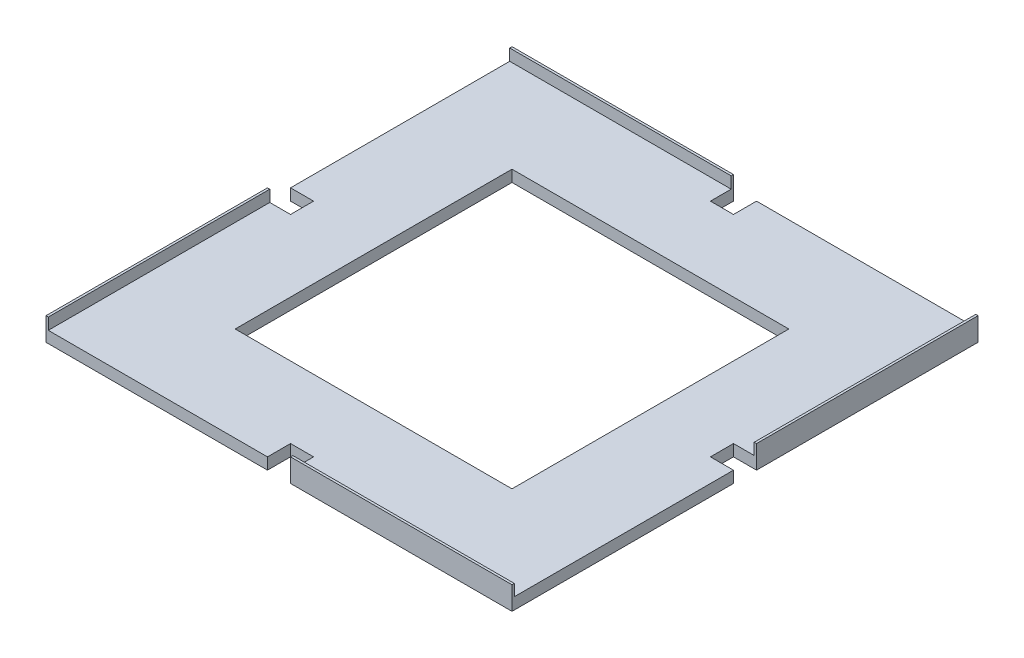
SolidWorks part; units mm, degrees
ref_plane "Front Plane" through (0, 0, 0) normal (0, 0, 1) x (1, 0, 0)
ref_plane "Top Plane" through (0, 0, 0) normal (0, 1, 0) x (1, 0, 0)
ref_plane "Right Plane" through (0, 0, 0) normal (1, 0, 0) x (0, 0, -1)
sketch "Sketch1" plane through (0, 0, 0) normal (0, 1, 0) x (1, 0, 0)
  line L0 (-91, 0) -> (91, 0) construction
  line L1 (101, -101) -> (5, -101)
  line L2 (101, -101) -> (101, -5)
  line L3 (101, 101) -> (5, 101)
  line L4 (-101, -101) -> (-101, -5)
  line L5 (101, -101) -> (-101, 101) construction
  line L6 (101, 101) -> (-101, -101) construction
  line L7 (-60, -60) -> (60, -60)
  line L8 (-60, -60) -> (-60, 60)
  line L9 (-60, 60) -> (60, 60)
  line L10 (60, -60) -> (60, 60)
  line L11 (-60, -60) -> (60, 60) construction
  line L12 (-60, 60) -> (60, -60) construction
  line L13 (0, 91) -> (0, -91) construction
  line L14 (-5, 101) -> (-5, 91)
  line L15 (-101, -5) -> (-91, -5)
  line L17 (-101, 5) -> (-91, 5)
  line L18 (-91, -5) -> (-91, 5)
  line L19 (101, 5) -> (101, 101)
  line L20 (-5, -101) -> (-101, -101)
  line L22 (5, 101) -> (5, 91)
  line L23 (-5, 91) -> (5, 91)
  line L24 (101, 5) -> (91, 5)
  line L26 (101, -5) -> (91, -5)
  line L27 (91, 5) -> (91, -5)
  line L28 (5, -101) -> (5, -91)
  line L30 (-5, -101) -> (-5, -91)
  line L31 (5, -91) -> (-5, -91)
  line L32 (-101, 5) -> (-101, 101)
  line L33 (-5, 101) -> (-101, 101)
  line L34 (-55, 0) -> (55, 0) construction
  point P0 (0, 0)
  point P6 (0, 0)
  point P34 (0, 0)
  dimension "D1" = 202
  dimension "D2" = 202
  dimension "D3" = 120
  dimension "D4" = 120
  dimension "D5" = 10
  dimension "D6" = 10
  dimension "D7" = 4
extrude "Boss-Extrude1" add sketch "Sketch1" along normal blind 5
sketch "Sketch2" plane through (0, 5, 0) normal (0, 1, 0) x (1, 0, 0)
  line L0 (101, -101) -> (101, -5) construction
  line L1 (5, -101) -> (101, -101)
  line L2 (5, -101) -> (5, -100)
  line L3 (5, -100) -> (101, -100)
  line L4 (101, -101) -> (101, -100)
  line L5 (-101, -5) -> (-100, -5)
  line L6 (-100, -5) -> (-100, -101)
  line L7 (-101, -5) -> (-101, -101)
  line L8 (-101, -101) -> (-100, -101)
  line L9 (-5, 101) -> (-5, 100)
  line L10 (-5, 100) -> (-101, 100)
  line L11 (-5, 101) -> (-101, 101)
  line L12 (-101, 101) -> (-101, 100)
  line L13 (101, 5) -> (100, 5)
  line L14 (100, 5) -> (100, 101)
  line L15 (101, 5) -> (101, 101)
  line L16 (101, 101) -> (100, 101)
  point P22 (0, 0)
  dimension "D1" = 1
  dimension "D2" = 4
extrude "Boss-Extrude2" add sketch "Sketch2" along normal blind 5
